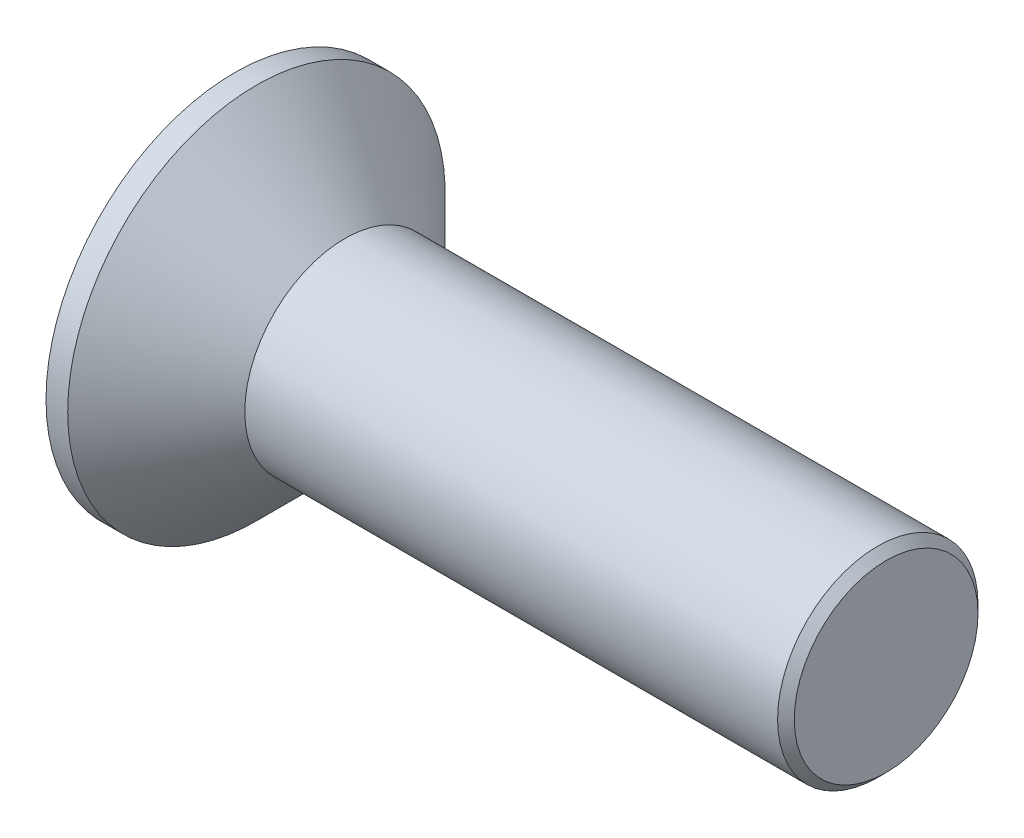
SolidWorks part; units mm, degrees
ref_plane "Plane1" through (0, 0, 0) normal (0, 0, 1) x (1, 0, 0)
ref_plane "Plane2" through (0, 0, 0) normal (0, 1, 0) x (1, 0, 0)
ref_plane "Plane3" through (0, 0, 0) normal (1, 0, 0) x (0, 0, -1)
sketch "BodySke" plane through (0, 0, 0) normal (0, 0, 1) x (1, 0, 0)
  line L0 (0, 0) -> (0, 5.65)
  line L1 (0, 5.65) -> (0.65, 5.65)
  line L2 (3.3, 3) -> (19.5, 3)
  line L3 (19.5, 3) -> (19.5, 0)
  line L4 (19.5, 0) -> (0, 0)
  line L5 (-6.35, 0) -> (82.55, 0) construction
  line L6 (3.3, -3) -> (19.5, -3) construction
  line L7 (0.65, -5.65) -> (3.3, -3) construction
  line L8 (0.65, 5.65) -> (3.3, 3)
  line L9 (0, -5.65) -> (0.65, -5.65) construction
  line L10 (4.3, 4.5875) -> (4.3, -4.9375) construction
  line L11 (11.5, 6.35) -> (11.5, -3.175) construction
  dimension "Diameter" = 6
  dimension "Length" = 19.5
  dimension "Head_ht" = 3.3
  dimension "Head_dia" = 11.3
  dimension "Head_ang" = 90
  dimension "D6" = 0.65
  dimension "Advance" = 1
  dimension "Thread_nom" = 8
revolve "Base-Revolve" add sketch "BodySke" angle 360 about L5
cosmetic thread "ThreadCosmetic" parameters "Thread_minor"=4.891
sketch "Sketch1" plane through (0, 0, 0) normal (-1, 0, 0) x (0, 0, 1)
  line L1 (0, -3) -> (2.5981, -1.5)
  line L2 (2.5981, -1.5) -> (2.5981, 1.5)
  line L3 (2.5981, 1.5) -> (0, 3)
  line L4 (0, 3) -> (-2.5981, 1.5)
  line L5 (-2.5981, 1.5) -> (-2.5981, -1.5)
  line L6 (-2.5981, -1.5) -> (0, -3)
  circle A0 centre (0, 0) radius 3 construction
  circle A1 centre (0, 0) radius 3 construction
  circle A2 centre (0, 0) radius 2.5981 construction
extrude "Cut-Extrude1" cut sketch "Sketch1" against normal blind 2
chamfer "Chamfer1" distance 0.25 angle 45 1 edges at (19.5, 0, 3)
